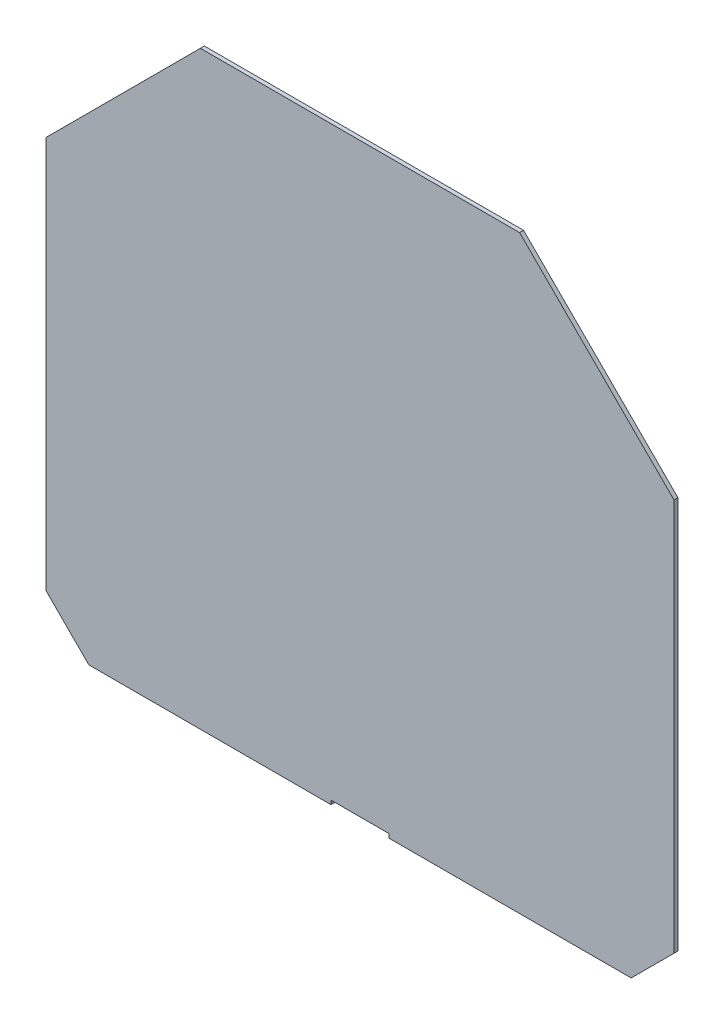
SolidWorks part; units mm, degrees
ref_plane "Front Plane" through (0, 0, 0) normal (0, 0, 1) x (1, 0, 0)
ref_plane "Top Plane" through (0, 0, 0) normal (0, 1, 0) x (1, 0, 0)
ref_plane "Right Plane" through (0, 0, 0) normal (1, 0, 0) x (0, 0, -1)
sketch "Sketch2" plane through (0, 0, 0) normal (0, 0, 1) x (1, 0, 0)
  line L13 (-22, -68) -> (22, -68)
  line L14 (22, -68) -> (22, -71)
  line L15 (22, -71) -> (205.3564, -71)
  line L16 (205.3564, -71) -> (237.8048, -38.5515)
  line L17 (237.8048, -38.5515) -> (237.8048, 258.7221)
  line L18 (237.8048, 258.7221) -> (120.8782, 375.6488)
  line L19 (120.8782, 375.6488) -> (-120.8782, 375.6488)
  line L20 (-120.8782, 375.6488) -> (-237.8048, 258.7221)
  line L21 (-237.8048, 258.7221) -> (-237.8048, -38.5515)
  line L22 (-237.8048, -38.5515) -> (-205.3564, -71)
  line L23 (-205.3564, -71) -> (-22, -71)
  line L24 (-22, -71) -> (-22, -68)
  line L25 (-22, -68) -> (22, -68)
  line L26 (22, -68) -> (22, -71)
  line L27 (22, -71) -> (205.3564, -71)
  line L28 (205.3564, -71) -> (237.8048, -38.5515)
  line L29 (237.8048, -38.5515) -> (237.8048, 258.7221)
  line L30 (237.8048, 258.7221) -> (120.8782, 375.6488)
  line L31 (120.8782, 375.6488) -> (-120.8782, 375.6488)
  line L32 (-120.8782, 375.6488) -> (-237.8048, 258.7221)
  line L33 (-237.8048, 258.7221) -> (-237.8048, -38.5515)
  line L34 (-237.8048, -38.5515) -> (-205.3564, -71)
  line L35 (-205.3564, -71) -> (-22, -71)
  line L36 (-22, -71) -> (-22, -68)
  dimension "D1" = 0
extrude "Boss-Extrude1" add sketch "Sketch2" along normal blind 3
